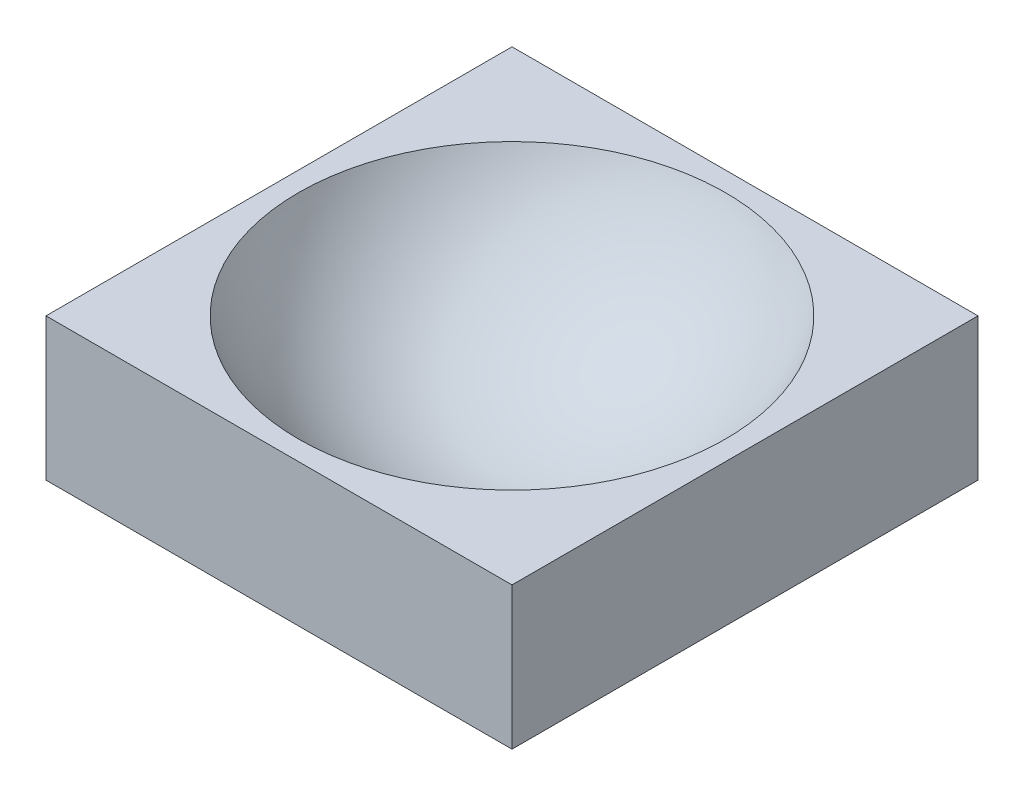
SolidWorks part; units mm, degrees
ref_plane "Front Plane" through (0, 0, 0) normal (0, 0, 1) x (1, 0, 0)
ref_plane "Top Plane" through (0, 0, 0) normal (0, 1, 0) x (1, 0, 0)
ref_plane "Right Plane" through (0, 0, 0) normal (1, 0, 0) x (0, 0, -1)
sketch "Sketch1" plane through (0, 0, 0) normal (0, 1, 0) x (1, 0, 0)
  line L0 (119.15, 119.15) -> (-119.15, -119.15) construction
  line L1 (119.15, 119.15) -> (-119.15, 119.15)
  line L2 (119.15, 119.15) -> (119.15, -119.15)
  line L3 (119.15, -119.15) -> (-119.15, -119.15)
  line L4 (-119.15, 119.15) -> (-119.15, -119.15)
  line L5 (-119.15, 119.15) -> (119.15, -119.15) construction
  point P5 (0, 0)
  point P6 (0, 0)
  dimension "D1" = 238.3
  dimension "D2" = 238.3
extrude "Boss-Extrude1" add sketch "Sketch1" along normal blind 72.7667
sketch "Sketch3" plane through (0, 0, 0) normal (0, 0, 1) x (1, 0, 0)
  line L0 (0, 0) -> (0, 10) construction
  line L1 (0, 10) -> (0, 119.15) construction
  line L2 (-119.15, 72.7667) -> (119.15, 72.7667) construction
  line L3 (-109.15, 72.7667) -> (0, 72.7667)
  line L4 (0, 72.7667) -> (0, 10)
  line L5 (0, 10) -> (0, 0.5535)
  arc A1 (0, 0.5535) -> (-109.15, 72.7667) centre (0, 119.15) cw
  dimension "D1" = 10
  dimension "D2" = 10
  dimension "D3" = 109.15
revolve "Cut-Revolve8" cut sketch "Sketch3" angle 360 about L4
equation "\"Diameter\" = 218.3mm"
equation "\"D1@Boss-Extrude1\"=\"Diameter\"/3"
equation "\"Pad\"= 10mm"
equation "\"D1@Sketch1\"=\"Diameter\"+2*\"Pad\""
equation "\"D2@Sketch1\"=\"Diameter\"+2*\"Pad\""
equation "\"D1@Sketch3\"=\"Pad\""
equation "\"D2@Sketch3\"=\"Pad\""
equation "\"D3@Sketch3\"=\"Diameter\"/2"
